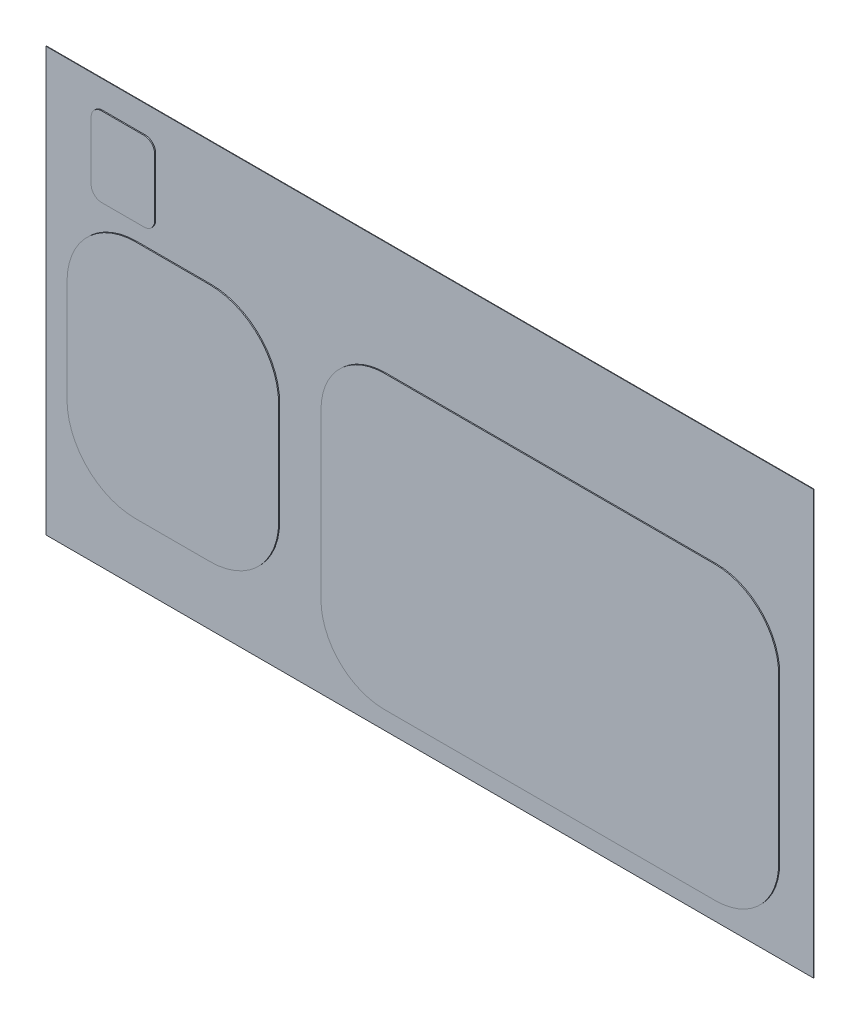
SolidWorks part; units mm, degrees
ref_plane "Front Plane" through (0, 0, 0) normal (0, 0, 1) x (1, 0, 0)
ref_plane "Top Plane" through (0, 0, 0) normal (0, 1, 0) x (1, 0, 0)
ref_plane "Right Plane" through (0, 0, 0) normal (1, 0, 0) x (0, 0, -1)
sketch "Sketch1" plane through (0, 0, 0) normal (0, 0, 1) x (1, 0, 0)
  line L1 (130000, -12500) -> (-15000, -12500)
  line L2 (130000, -12500) -> (130000, 67500)
  line L3 (130000, 67500) -> (-15000, 67500)
  line L4 (-15000, -12500) -> (-15000, 67500)
  dimension "D1" = 12500
  dimension "D2" = 80000
  dimension "D3" = 15000
  dimension "D4" = 145000
extrude "Extrude1" add sketch "Sketch1" against normal blind 300
sketch "Sketch2" plane through (0, 0, 0) normal (0, 0, 1) x (1, 0, 0)
  line L4 (37145.0577, 34139.6336) -> (37145.0577, 3109.6336)
  line L5 (49145.0577, -8890.3664) -> (111645.0577, -8890.3664)
  line L6 (123645.0577, 3109.6336) -> (123645.0577, 34139.6336)
  line L7 (111645.0577, 46139.6336) -> (49145.0577, 46139.6336)
  line L8 (37145.0577, 34139.6336) -> (37145.0577, 3109.6336)
  line L9 (49145.0577, -8890.3664) -> (111645.0577, -8890.3664)
  line L10 (123645.0577, 3109.6336) -> (123645.0577, 34139.6336)
  line L11 (111645.0577, 46139.6336) -> (49145.0577, 46139.6336)
  line L12 (16145.0577, 44139.6336) -> (2145.0577, 44139.6336)
  line L13 (-10854.9423, 31139.6336) -> (-10854.9423, 11839.6336)
  line L14 (2145.0577, -1160.3664) -> (16145.0577, -1160.3664)
  line L15 (29145.0577, 11839.6336) -> (29145.0577, 31139.6336)
  line L16 (16145.0577, 44139.6336) -> (2145.0577, 44139.6336)
  line L17 (-10854.9423, 31139.6336) -> (-10854.9423, 11839.6336)
  line L18 (2145.0577, -1160.3664) -> (16145.0577, -1160.3664)
  line L19 (29145.0577, 11839.6336) -> (29145.0577, 31139.6336)
  line L124 (-6301.0005, 60369.7277) -> (-6301.0005, 49369.7277)
  line L125 (-4301.0005, 47369.7277) -> (3698.9995, 47369.7277)
  line L126 (5698.9995, 49369.7277) -> (5698.9995, 60369.7277)
  line L127 (3698.9995, 62369.7277) -> (-4301.0005, 62369.7277)
  line L128 (-6301.0005, 60369.7277) -> (-6301.0005, 49369.7277)
  line L129 (-4301.0005, 47369.7277) -> (3698.9995, 47369.7277)
  line L130 (5698.9995, 49369.7277) -> (5698.9995, 60369.7277)
  line L131 (3698.9995, 62369.7277) -> (-4301.0005, 62369.7277)
  arc A4 (49145.0577, 46139.6336) -> (37145.0577, 34139.6336) centre (49145.0577, 34139.6336) ccw
  arc A5 (37145.0577, 3109.6336) -> (49145.0577, -8890.3664) centre (49145.0577, 3109.6336) ccw
  arc A6 (111645.0577, -8890.3664) -> (123645.0577, 3109.6336) centre (111645.0577, 3109.6336) ccw
  arc A7 (123645.0577, 34139.6336) -> (111645.0577, 46139.6336) centre (111645.0577, 34139.6336) ccw
  arc A8 (49145.0577, 46139.6336) -> (37145.0577, 34139.6336) centre (49145.0577, 34139.6336) ccw
  arc A9 (37145.0577, 3109.6336) -> (49145.0577, -8890.3664) centre (49145.0577, 3109.6336) ccw
  arc A10 (111645.0577, -8890.3664) -> (123645.0577, 3109.6336) centre (111645.0577, 3109.6336) ccw
  arc A11 (123645.0577, 34139.6336) -> (111645.0577, 46139.6336) centre (111645.0577, 34139.6336) ccw
  arc A12 (29145.0577, 31139.6336) -> (16145.0577, 44139.6336) centre (16145.0577, 31139.6336) ccw
  arc A13 (2145.0577, 44139.6336) -> (-10854.9423, 31139.6336) centre (2145.0577, 31139.6336) ccw
  arc A14 (-10854.9423, 11839.6336) -> (2145.0577, -1160.3664) centre (2145.0577, 11839.6336) ccw
  arc A15 (16145.0577, -1160.3664) -> (29145.0577, 11839.6336) centre (16145.0577, 11839.6336) ccw
  arc A16 (29145.0577, 31139.6336) -> (16145.0577, 44139.6336) centre (16145.0577, 31139.6336) ccw
  arc A17 (2145.0577, 44139.6336) -> (-10854.9423, 31139.6336) centre (2145.0577, 31139.6336) ccw
  arc A18 (-10854.9423, 11839.6336) -> (2145.0577, -1160.3664) centre (2145.0577, 11839.6336) ccw
  arc A19 (16145.0577, -1160.3664) -> (29145.0577, 11839.6336) centre (16145.0577, 11839.6336) ccw
  arc A124 (-4301.0005, 62369.7277) -> (-6301.0005, 60369.7277) centre (-4301.0005, 60369.7277) ccw
  arc A125 (-6301.0005, 49369.7277) -> (-4301.0005, 47369.7277) centre (-4301.0005, 49369.7277) ccw
  arc A126 (3698.9995, 47369.7277) -> (5698.9995, 49369.7277) centre (3698.9995, 49369.7277) ccw
  arc A127 (5698.9995, 60369.7277) -> (3698.9995, 62369.7277) centre (3698.9995, 60369.7277) ccw
  arc A128 (-4301.0005, 62369.7277) -> (-6301.0005, 60369.7277) centre (-4301.0005, 60369.7277) ccw
  arc A129 (-6301.0005, 49369.7277) -> (-4301.0005, 47369.7277) centre (-4301.0005, 49369.7277) ccw
  arc A130 (3698.9995, 47369.7277) -> (5698.9995, 49369.7277) centre (3698.9995, 49369.7277) ccw
  arc A131 (5698.9995, 60369.7277) -> (3698.9995, 62369.7277) centre (3698.9995, 60369.7277) ccw
  dimension "D1" = 0
  dimension "D2" = 0
  dimension "D3" = 0
extrude "Cut-Extrude1" cut sketch "Sketch2" against normal blind 200 flip side to cut
